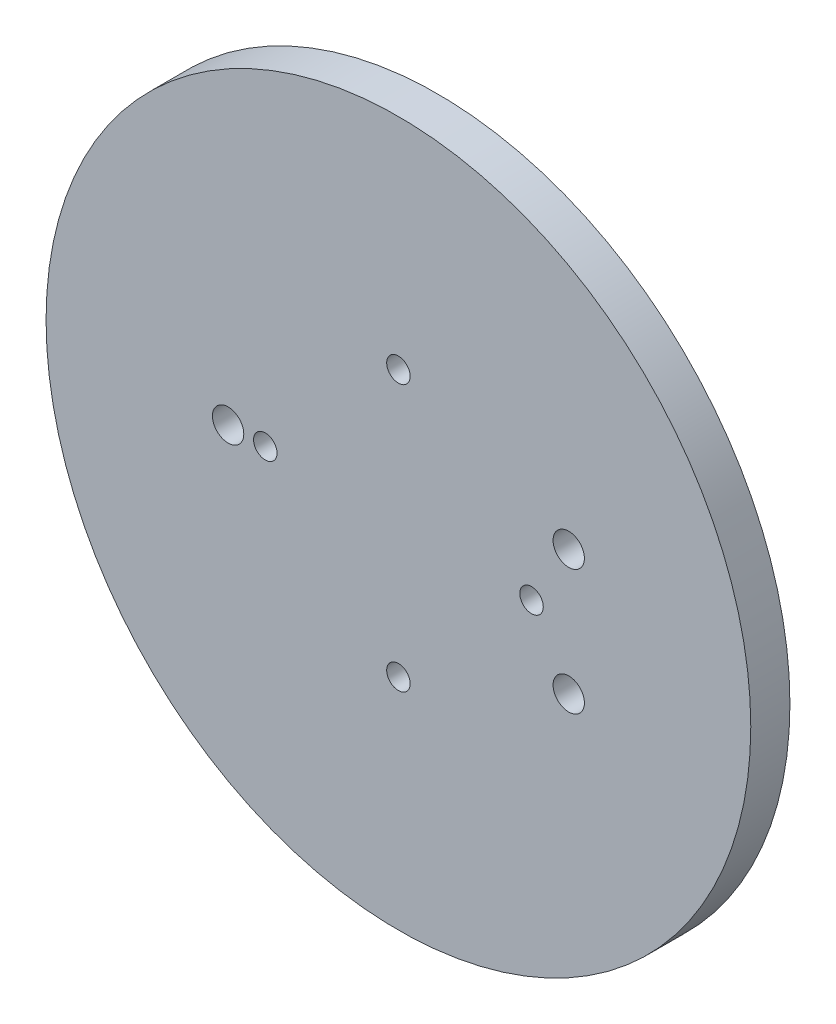
SolidWorks part; units mm, degrees
ref_plane "Front Plane" through (0, 0, 0) normal (0, 0, 1) x (1, 0, 0)
ref_plane "Top Plane" through (0, 0, 0) normal (0, 1, 0) x (1, 0, 0)
ref_plane "Right Plane" through (0, 0, 0) normal (1, 0, 0) x (0, 0, -1)
sketch "Sketch1" plane through (0, 0, 0) normal (0, 0, 1) x (1, 0, 0)
  line L0 (0, 57.9566) -> (0, -58.0749) construction
  line L1 (-57.4014, 0) -> (57.4014, 0) construction
  circle A0 centre (0, 0) radius 45
  point P7 (0, 0)
  dimension "D1" = 90
extrude "Boss-Extrude1" add sketch "Sketch1" along normal blind 5
sketch "Sketch3" plane through (0, 0, 5) normal (0, 0, 1) x (1, 0, 0)
  line L0 (-73.1999, 0) -> (75.1467, 0) construction
  line L1 (0, 77.103) -> (0, -77.103) construction
  circle A0 centre (-21.75, 0) radius 2
  circle A1 centre (21.75, 8) radius 2
  circle A2 centre (21.75, -8) radius 2
  circle A3 centre (0, 17) radius 1.5
  circle A4 centre (17, 0) radius 1.5
  circle A5 centre (0, -17) radius 1.5
  circle A6 centre (-17, 0) radius 1.5
  circle A7 centre (0, 0) radius 45 construction
  point P5 (0, 0)
  point P23 (0, 0)
  dimension "D1" = 4
  dimension "D3" = 8
  dimension "D4" = 8
  dimension "D6" = 3
  dimension "D9" = 17
  dimension "D2" = 21.75
  dimension "D5" = 21.75
  dimension "D7" = 17
  dimension "D10" = 17
  dimension "D8" = 4
extrude "Cut-Extrude1" cut sketch "Sketch3" against normal blind 10
